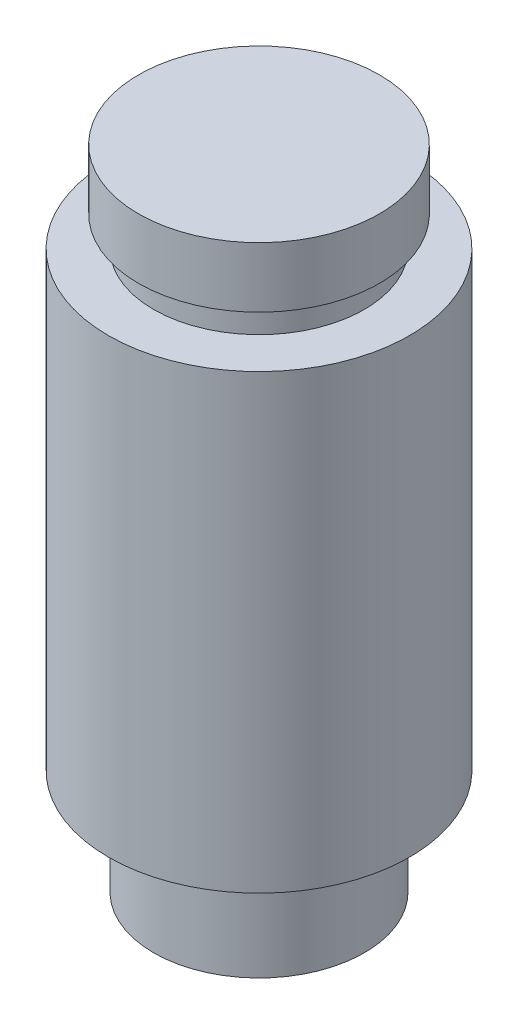
SolidWorks part; units mm, degrees
ref_plane "Front Plane" through (0, 0, 0) normal (0, 0, 1) x (1, 0, 0)
ref_plane "Top Plane" through (0, 0, 0) normal (0, 1, 0) x (1, 0, 0)
ref_plane "Right Plane" through (0, 0, 0) normal (1, 0, 0) x (0, 0, -1)
sketch "Sketch1" plane through (0, 0, 0) normal (0, 0, 1) x (1, 0, 0)
  line L0 (0, 0) -> (0, 54.61)
  line L1 (0, 54.61) -> (10.16, 54.61)
  line L2 (10.16, 54.61) -> (10.16, 49.53)
  line L3 (10.16, 49.53) -> (8.89, 49.53)
  line L4 (8.89, 49.53) -> (8.89, 46.99)
  line L5 (8.89, 46.99) -> (12.7, 46.99)
  line L6 (12.7, 46.99) -> (12.7, 8.89)
  line L7 (12.7, 8.89) -> (8.89, 8.89)
  line L8 (8.89, 8.89) -> (8.89, 0)
  line L9 (8.89, 0) -> (0, 0)
  dimension "D1" = 8.89
  dimension "D2" = 12.7
  dimension "D3" = 10.16
  dimension "D4" = 38.1
  dimension "D5" = 8.89
  dimension "D6" = 2.54
  dimension "D7" = 5.08
  dimension "D8" = 8.89
revolve "Revolve1" add sketch "Sketch1" angle 360 about L0
